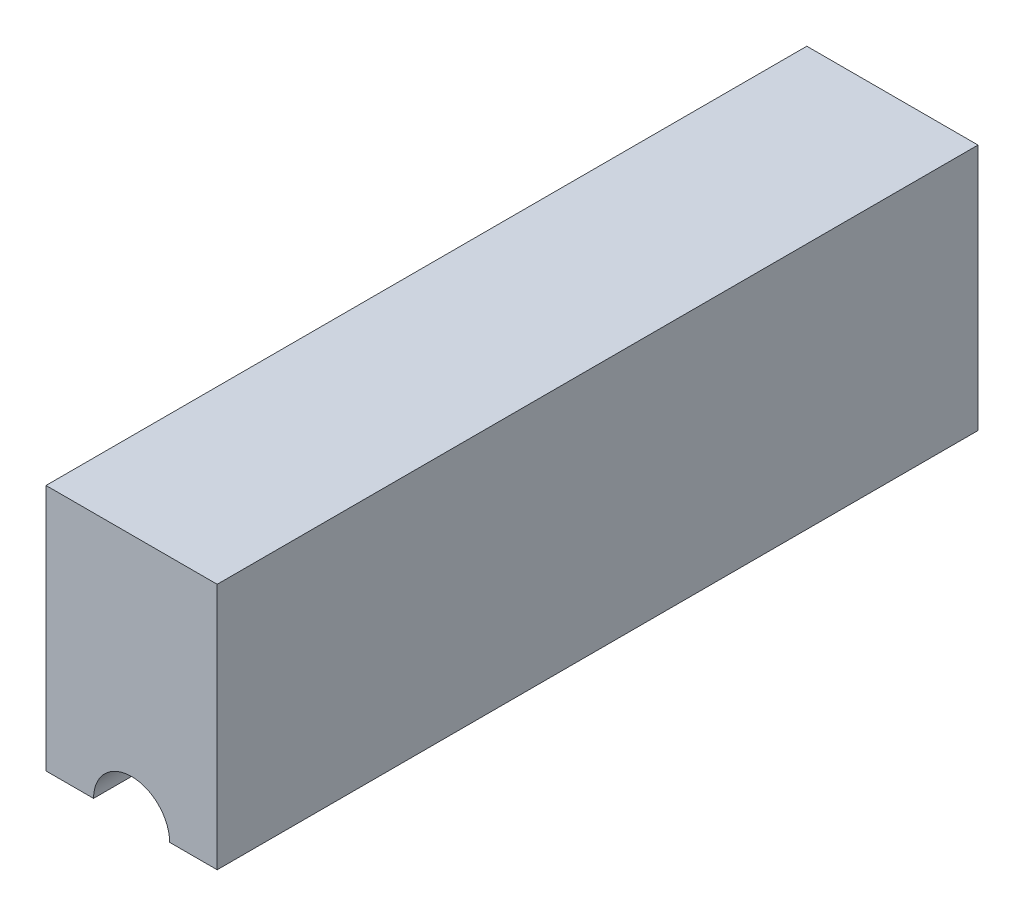
SolidWorks part; units mm, degrees
ref_plane "Front" through (0, 0, 0) normal (0, 0, 1) x (1, 0, 0)
ref_plane "Top" through (0, 0, 0) normal (0, 1, 0) x (1, 0, 0)
ref_plane "Right" through (0, 0, 0) normal (1, 0, 0) x (0, 0, -1)
sketch "Sketch1" plane through (0, 0, 0) normal (0, 0, 1) x (1, 0, 0)
  line L0 (32.5, 0) -> (45, 0)
  line L1 (0, 0) -> (12.5, 0)
  line L2 (0, 0) -> (0, 65)
  line L3 (0, 65) -> (45, 65)
  line L4 (45, 0) -> (45, 65)
  arc A0 (32.5, 0) -> (12.5, 0) centre (22.5, 0) ccw
  dimension "D3" = 10
  dimension "D1" = 45
  dimension "D2" = 65
  dimension "D4" = 22.5
extrude "Base-Extrude" add sketch "Sketch1" along normal mid plane 200
